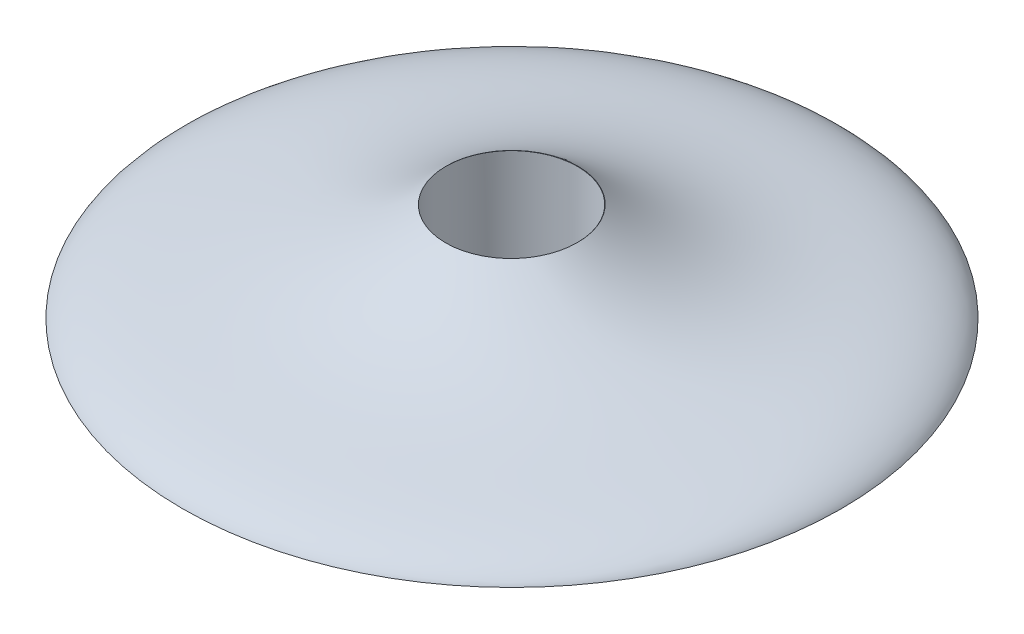
SolidWorks part; units mm, degrees
material "ABS"
ref_plane "Front" through (0, 0, 0) normal (0, 0, 1) x (1, 0, 0)
ref_plane "Top" through (0, 0, 0) normal (0, 1, 0) x (1, 0, 0)
ref_plane "Right" through (0, 0, 0) normal (1, 0, 0) x (0, 0, -1)
sketch "草图2" plane through (0, 0, 0) normal (1, 0, 0) x (0, 0, -1)
  line L0 (-77.0266, 21.8997) -> (-77.0266, -8.1003)
  line L1 (-77.0266, -8.1003) -> (22.9734, -8.1003)
  line L2 (-77.0266, 21.8997) -> (-57.0266, 21.8997)
  line L3 (22.9734, -8.1003) -> (19.9993, -2.4933) construction
  line L4 (19.9993, -2.4933) -> (-0.0221, 5.0483) construction
  line L5 (-0.0221, 5.0483) -> (-26.4374, -4.1151) construction
  line L6 (-26.4374, -4.1151) -> (-57.0266, 21.8997) construction
  spline S0 degree 4 poles (22.9734, -8.1003) (19.9993, -2.4933) (-0.0221, 5.0483) (-26.4374, -4.1151) (-57.0266, 21.8997) knots 0 0 0 0 0 1 1 1 1 1
  point P7 (-26.4374, -4.1151)
  point P8 (19.9993, -2.4933)
  dimension "D1" = 30
  dimension "D2" = 100
  dimension "D3" = 20
revolve "旋转1" add sketch "草图2" angle 360 about L0
sketch "草图3" plane through (0, 21.8997, 0) normal (0, 1, 0) x (1, 0, 0)
  circle A0 centre (0, -77.1524) radius 20
extrude "切除-拉伸1" cut sketch "草图3" against normal blind 58
